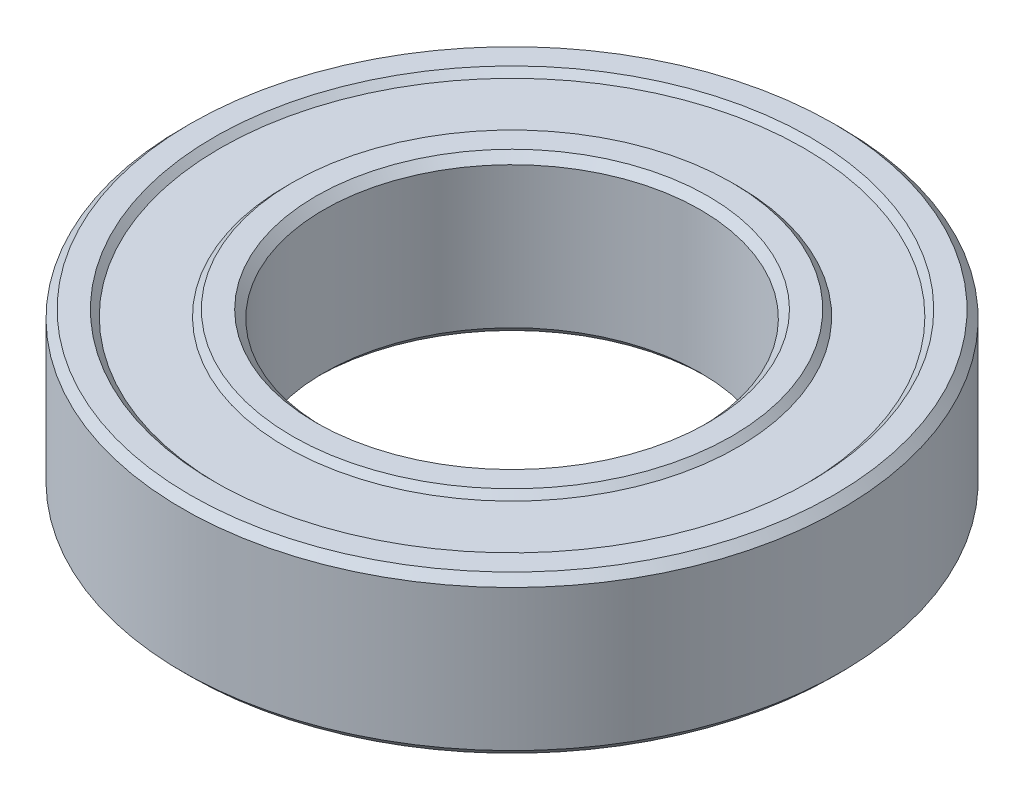
SolidWorks part; units mm, degrees
material "Stainless Steel (ferritic)"
ref_plane "Front Plane" through (0, 0, 0) normal (0, 0, 1) x (1, 0, 0)
ref_plane "Top Plane" through (0, 0, 0) normal (0, 1, 0) x (1, 0, 0)
ref_plane "Right Plane" through (0, 0, 0) normal (1, 0, 0) x (0, 0, -1)
sketch "Sketch1" plane through (0, 0, 0) normal (0, 0, 1) x (1, 0, 0)
  line L0 (0, -1.3494) -> (0, 70.5256) construction
  line L1 (6, 2.25) -> (6, -2.25)
  line L2 (6, -2.25) -> (6.25, -2.5)
  line L3 (6.25, -2.5) -> (7, -2.5)
  line L4 (7, -2.5) -> (7.2, -2.3)
  line L5 (7.2, -2.3) -> (9.3, -2.3)
  line L6 (9.3, -2.3) -> (9.5, -2.5)
  line L7 (9.5, -2.5) -> (10.25, -2.5)
  line L8 (10.25, -2.5) -> (10.5, -2.25)
  line L9 (10.5, -2.25) -> (10.5, 2.25)
  line L10 (10.5, 2.25) -> (10.25, 2.5)
  line L11 (10.25, 2.5) -> (9.5, 2.5)
  line L12 (9.5, 2.5) -> (9.3, 2.3)
  line L13 (9.3, 2.3) -> (7.2, 2.3)
  line L14 (7.2, 2.3) -> (7, 2.5)
  line L15 (7, 2.5) -> (6.25, 2.5)
  line L16 (6.25, 2.5) -> (6, 2.25)
  line L17 (0, 0) -> (6, 0) construction
  dimension "D1" = 6
  dimension "D2" = 5
  dimension "D3" = 0.25
  dimension "D4" = 0.2
  dimension "D5" = 10.5
  dimension "D6" = 0.75
revolve "Revolve1" add sketch "Sketch1" angle 360 about L0
